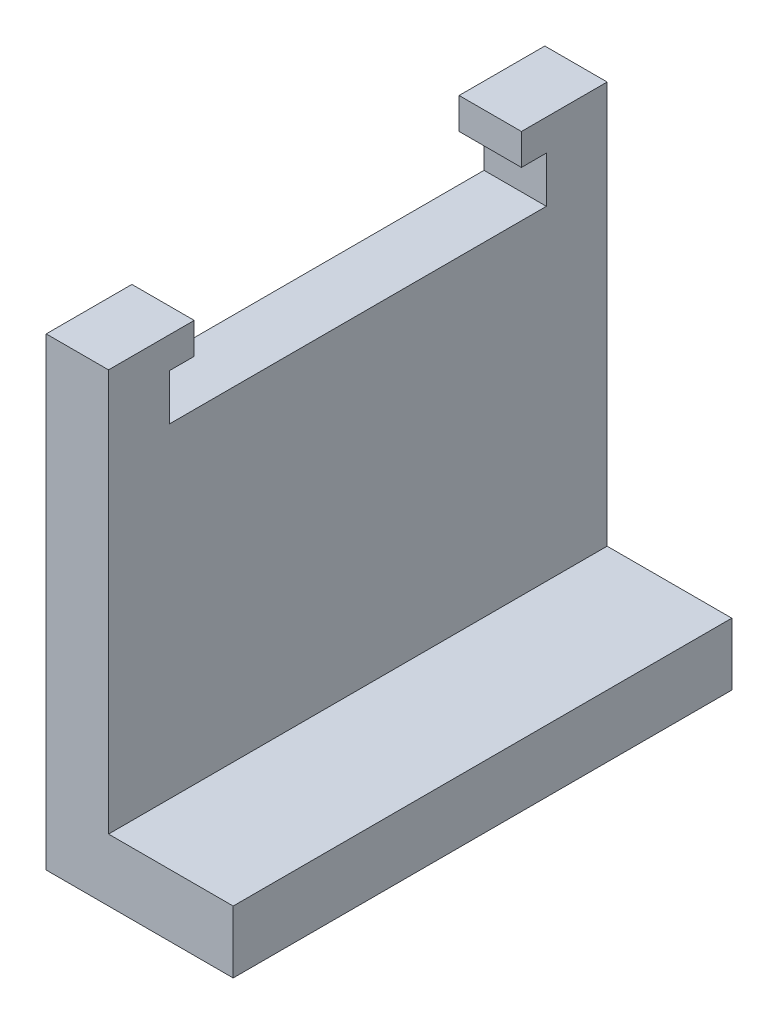
SolidWorks part; units mm, degrees
ref_plane "Front Plane" through (0, 0, 0) normal (0, 0, 1) x (1, 0, 0)
ref_plane "Top Plane" through (0, 0, 0) normal (0, 1, 0) x (1, 0, 0)
ref_plane "Right Plane" through (0, 0, 0) normal (1, 0, 0) x (0, 0, -1)
sketch "Sketch1" plane through (0, 0, 0) normal (1, 0, 0) x (0, 0, -1)
  line L0 (0, 0) -> (80, 0)
  line L1 (80, 0) -> (80, 74.5)
  line L2 (80, 74.5) -> (66.25, 74.5)
  line L3 (66.25, 74.5) -> (66.25, 69.5)
  line L4 (66.25, 69.5) -> (70.25, 69.5)
  line L5 (70.25, 69.5) -> (70.25, 62.1)
  line L6 (70.25, 62.1) -> (9.75, 62.1)
  line L7 (9.75, 62.1) -> (9.75, 69.5)
  line L8 (9.75, 69.5) -> (13.75, 69.5)
  line L9 (13.75, 69.5) -> (13.75, 74.5)
  line L10 (13.75, 74.5) -> (0, 74.5)
  line L11 (0, 74.5) -> (0, 0)
  line L12 (40, 0) -> (40, 62.1) construction
  dimension "D1" = 5
  dimension "D2" = 7.4
  dimension "D3" = 60.5
  dimension "D4" = 80
  dimension "D5" = 74.5
  dimension "D6" = 4
extrude "Boss-Extrude1" add sketch "Sketch1" along normal blind 10
sketch "Sketch2" plane through (10, 0, 0) normal (1, 0, 0) x (0, 0, -1)
  line L0 (80, 0) -> (80, 74.5) construction
  line L1 (0, 0) -> (80, 0)
  line L2 (0, 0) -> (0, 10)
  line L3 (0, 10) -> (80, 10)
  line L4 (80, 0) -> (80, 10)
  dimension "D1" = 10
extrude "Boss-Extrude2" add sketch "Sketch2" along normal blind 20
